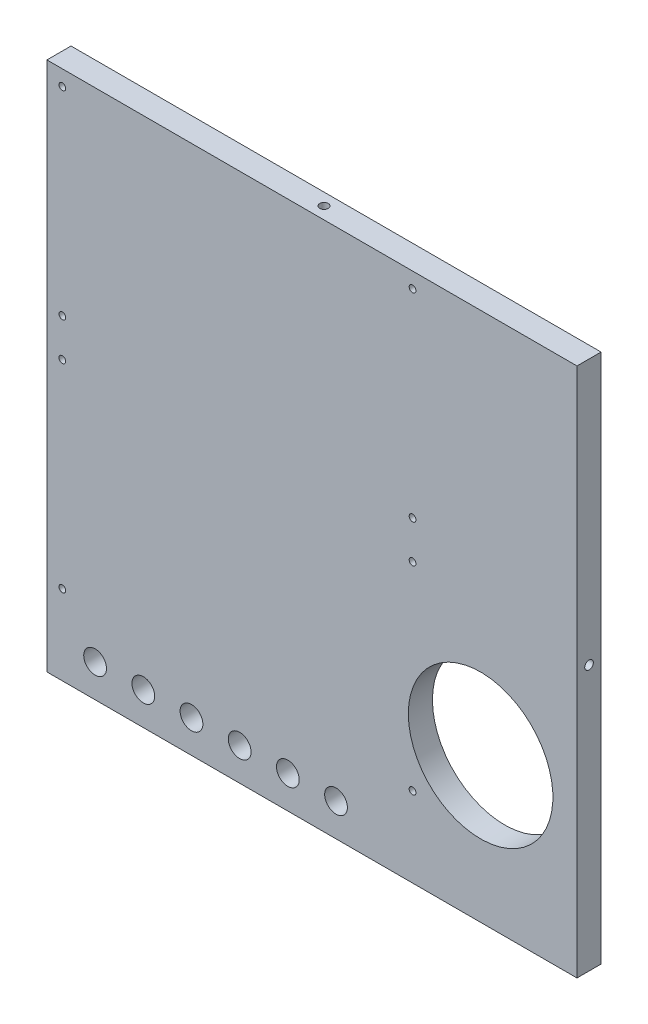
SolidWorks part; units mm, degrees
ref_plane "Front Plane" through (0, 0, 0) normal (0, 0, 1) x (1, 0, 0)
ref_plane "Top Plane" through (0, 0, 0) normal (0, 1, 0) x (1, 0, 0)
ref_plane "Right Plane" through (0, 0, 0) normal (1, 0, 0) x (0, 0, -1)
sketch "Sketch1" plane through (0, 0, 0) normal (0, 0, 1) x (1, 0, 0)
  line L1 (69.85, -69.85) -> (-69.85, -69.85)
  line L2 (69.85, -69.85) -> (69.85, 69.85)
  line L3 (69.85, 69.85) -> (-69.85, 69.85)
  line L4 (-69.85, -69.85) -> (-69.85, 69.85)
  line L5 (69.85, -69.85) -> (-69.85, 69.85) construction
  line L6 (69.85, 69.85) -> (-69.85, -69.85) construction
  point P0 (0, 0)
  dimension "D1" = 139.7
  dimension "D2" = 139.7
extrude "Boss-Extrude1" add sketch "Sketch1" along normal blind 6.35 contours L3 L4 L1 L2
hole_wizard "#4-40 Tapped Hole1" positions "Sketch2" profile "Sketch3" tap size "#4-40" standard "ANSI Inch"
sketch "Sketch2" plane through (0, 69.85, 0) normal (0, 1, 0) x (1, 0, 0)
  line L0 (69.85, -6.35) -> (-69.85, -6.35) construction
  line L1 (-69.85, -6.35) -> (-69.85, 0) construction
  point P0 (0, -3.175)
  dimension "D1" = 3.175
  dimension "D2" = 69.85
sketch "Sketch3" plane through (0, 69.85, 3.175) normal (1, 0, 0) x (0, 0, 1)
  line L0 (0, 0) -> (0, 8.2738)
  line L1 (0, 8.2738) -> (1.1303, 7.5946)
  line L2 (1.1303, 7.5946) -> (1.1303, 0)
  line L5 (1.1303, 0) -> (0, 0)
  line L10 (0, 8.2738) -> (-1.1303, 7.5946) construction
  line L11 (0, -6.35) -> (0, 107.95) construction
  dimension "Tap Drill Dia." = 2.2606
  dimension "Tap Drill Depth" = 7.5946
  dimension "Drill Angle" = 118
cosmetic thread "Hole Thread1" parameters "D1"=5.6896, "D2"=2.8448
hole_wizard "#4-40 Tapped Hole2" positions "Sketch5" profile "Sketch6" tap size "#4-40" standard "ANSI Inch"
sketch "Sketch5" plane through (69.85, 0, 0) normal (1, 0, 0) x (0, 0, -1)
  line L0 (0, -69.85) -> (0, 69.85) construction
  line L1 (-6.35, -69.85) -> (0, -69.85) construction
  point P0 (-3.175, 0)
  dimension "D1" = 3.175
  dimension "D2" = 69.85
sketch "Sketch6" plane through (69.85, 0, 3.175) normal (0, 1, 0) x (0, 0, -1)
  line L0 (0, 0) -> (0, 8.2738)
  line L1 (0, 8.2738) -> (1.1303, 7.5946)
  line L2 (1.1303, 7.5946) -> (1.1303, 0)
  line L5 (1.1303, 0) -> (0, 0)
  line L10 (0, 8.2738) -> (-1.1303, 7.5946) construction
  line L11 (0, -6.35) -> (0, 107.95) construction
  dimension "Tap Drill Dia." = 2.2606
  dimension "Tap Drill Depth" = 7.5946
  dimension "Drill Angle" = 118
cosmetic thread "Hole Thread2" parameters "D1"=5.6896, "D2"=2.8448
hole_wizard "#4-40 Tapped Hole3" positions "Sketch7" profile "Sketch8" tap size "#4-40" standard "ANSI Inch"
sketch "Sketch7" plane through (0, -69.85, 0) normal (0, -1, 0) x (-1, 0, 0)
  line L0 (-69.85, 0) -> (69.85, 0) construction
  point P0 (0, -3.175)
  dimension "D1" = 3.175
sketch "Sketch8" plane through (0, -69.85, 3.175) normal (1, 0, 0) x (0, 0, -1)
  line L0 (0, 0) -> (0, 8.2738)
  line L1 (0, 8.2738) -> (1.1303, 7.5946)
  line L2 (1.1303, 7.5946) -> (1.1303, 0)
  line L5 (1.1303, 0) -> (0, 0)
  line L10 (0, 8.2738) -> (-1.1303, 7.5946) construction
  line L11 (0, -6.35) -> (0, 107.95) construction
  dimension "Tap Drill Dia." = 2.2606
  dimension "Tap Drill Depth" = 7.5946
  dimension "Drill Angle" = 118
cosmetic thread "Hole Thread3" parameters "D1"=5.6896, "D2"=2.8448
hole_wizard "#4-40 Tapped Hole4" positions "Sketch9" profile "Sketch10" tap size "#4-40" standard "ANSI Inch"
sketch "Sketch9" plane through (-69.85, 0, 0) normal (-1, 0, 0) x (0, 0, 1)
  line L0 (0, -69.85) -> (0, 69.85) construction
  point P0 (3.175, 0)
  dimension "D1" = 3.175
sketch "Sketch10" plane through (-69.85, 0, 3.175) normal (0, 1, 0) x (0, 0, 1)
  line L0 (0, 0) -> (0, 8.2738)
  line L1 (0, 8.2738) -> (1.1303, 7.5946)
  line L2 (1.1303, 7.5946) -> (1.1303, 0)
  line L5 (1.1303, 0) -> (0, 0)
  line L10 (0, 8.2738) -> (-1.1303, 7.5946) construction
  line L11 (0, -6.35) -> (0, 107.95) construction
  dimension "Tap Drill Dia." = 2.2606
  dimension "Tap Drill Depth" = 7.5946
  dimension "Drill Angle" = 118
cosmetic thread "Hole Thread4" parameters "D1"=5.6896, "D2"=2.8448
sketch "Sketch11" plane through (0, 0, 0) normal (0, 0, -1) x (-1, 0, 0)
  line L1 (-69.85, -69.85) -> (-69.85, 69.85) construction
  line L2 (-69.85, -69.85) -> (69.85, -69.85) construction
  circle A0 centre (-44.45, -31.75) radius 19.05
  dimension "D1" = 38.1
  dimension "D2" = 25.4
  dimension "D3" = 38.1
extrude "Cut-Extrude1" cut sketch "Sketch11" against normal through all
hole_wizard "#2-56 Tapped Hole1" positions "Sketch12" profile "Sketch13" tap size "#2-56" standard "ANSI Inch"
sketch "Sketch12" plane through (0, 0, 6.35) normal (0, 0, 1) x (1, 0, 0)
  line L0 (69.85, 69.85) -> (-69.85, 69.85) construction
  line L1 (-69.85, -69.85) -> (-69.85, 69.85) construction
  point P0 (-65.786, 65.786)
  point P2 (26.514, 65.786)
  point P4 (-65.786, 13.486)
  point P6 (26.514, 13.486)
  point P8 (-65.786, 3.486)
  point P10 (26.514, 3.486)
  point P12 (-65.786, -48.814)
  point P14 (26.514, -48.814)
  dimension "D1" = 4.064
  dimension "D2" = 4.064
  dimension "D3" = 4.064
  dimension "D4" = 92.3
  dimension "D5" = 4.064
  dimension "D6" = 52.3
  dimension "D7" = 52.3
  dimension "D8" = 92.3
  dimension "D9" = 4.064
  dimension "D10" = 10
  dimension "D11" = 4.064
  dimension "D12" = 52.3
  dimension "D13" = 92.3
  dimension "D14" = 0
  dimension "D15" = 0
  dimension "D16" = 92.3
sketch "Sketch13" plane through (-65.786, 65.786, 6.35) normal (1, 0, 0) x (0, -1, 0)
  line L0 (0, 0) -> (0, 6.2746)
  line L1 (0, 6.2746) -> (0.889, 5.7404)
  line L2 (0.889, 5.7404) -> (0.889, 0)
  line L5 (0.889, 0) -> (0, 0)
  line L10 (0, 6.2746) -> (-0.889, 5.7404) construction
  line L11 (0, -6.35) -> (0, 107.95) construction
  dimension "Tap Drill Dia." = 1.778
  dimension "Tap Drill Depth" = 5.7404
  dimension "Drill Angle" = 118
cosmetic thread "Hole Thread6" parameters "D1"=4.3688, "D2"=2.1844
cosmetic thread "Hole Thread7" parameters "D1"=4.3688, "D2"=2.1844
cosmetic thread "Hole Thread8" parameters "D1"=4.3688, "D2"=2.1844
cosmetic thread "Hole Thread9" parameters "D1"=4.3688, "D2"=2.1844
cosmetic thread "Hole Thread10" parameters "D1"=4.3688, "D2"=2.1844
cosmetic thread "Hole Thread11" parameters "D1"=4.3688, "D2"=2.1844
cosmetic thread "Hole Thread12" parameters "D1"=4.3688, "D2"=2.1844
cosmetic thread "Hole Thread13" parameters "D1"=4.3688, "D2"=2.1844
hole_wizard "#2-56 Tapped Hole2" positions "Sketch14" profile "Sketch15" tap size "#2-56" standard "ANSI Inch"
sketch "Sketch14" plane through (0, 0, 0) normal (0, 0, -1) x (-1, 0, 0)
  line L0 (69.85, -69.85) -> (69.85, 69.85) construction
  line L1 (-69.85, 69.85) -> (69.85, 69.85) construction
  point P0 (44.45, 44.45)
  point P2 (44.45, -24.13)
  point P4 (-24.13, -24.13)
  point P6 (-24.13, 44.45)
  dimension "D1" = 68.58
  dimension "D2" = 25.4
  dimension "D3" = 68.58
  dimension "D4" = 25.4
  dimension "D5" = 25.4
  dimension "D6" = 0
  dimension "D7" = 0
sketch "Sketch15" plane through (-44.45, 44.45, 0) normal (1, 0, 0) x (0, 1, 0)
  line L0 (0, 0) -> (0, 6.2746)
  line L1 (0, 6.2746) -> (0.889, 5.7404)
  line L2 (0.889, 5.7404) -> (0.889, 0)
  line L5 (0.889, 0) -> (0, 0)
  line L10 (0, 6.2746) -> (-0.889, 5.7404) construction
  line L11 (0, -6.35) -> (0, 107.95) construction
  dimension "Tap Drill Dia." = 1.778
  dimension "Tap Drill Depth" = 5.7404
  dimension "Drill Angle" = 118
cosmetic thread "Hole Thread14" parameters "D1"=4.3688, "D2"=2.1844
cosmetic thread "Hole Thread15" parameters "D1"=4.3688, "D2"=2.1844
cosmetic thread "Hole Thread16" parameters "D1"=4.3688, "D2"=2.1844
cosmetic thread "Hole Thread17" parameters "D1"=4.3688, "D2"=2.1844
hole_wizard "Ø6.0mm Dowel Hole1" positions "Sketch16" profile "Sketch17" hole size "Ø6.0" standard "ANSI Metric" end condition through all
sketch "Sketch16" plane through (0, 0, 6.35) normal (0, 0, 1) x (1, 0, 0)
  line L0 (69.85, -69.85) -> (-69.85, -69.85) construction
  line L1 (-69.85, -69.85) -> (-69.85, 69.85) construction
  point P0 (-57.15, -61.214)
  point P13 (-44.45, -61.214)
  point P14 (-31.75, -61.214)
  point P15 (-19.05, -61.214)
  point P16 (-6.35, -61.214)
  point P22 (-44.45, -61.214)
  point P23 (-31.75, -61.214)
  point P24 (-19.05, -61.214)
  point P25 (-6.35, -61.214)
  point P26 (6.35, -61.214)
  dimension "D1" = 8.636
  dimension "D2" = 12.7
  dimension "D3" = 5
sketch "Sketch17" plane through (-57.15, -61.214, 6.35) normal (1, 0, 0) x (0, -1, 0)
  line L0 (0, 0) -> (0, 6.35)
  line L1 (0, 6.35) -> (3, 6.35)
  line L2 (3, 6.35) -> (3, 0)
  line L5 (3, 0) -> (0, 0)
  line L11 (0, -6.35) -> (0, 107.95) construction
  dimension "Thru Hole Dia." = 6
  dimension "Thru Hole Depth" = 6.35
